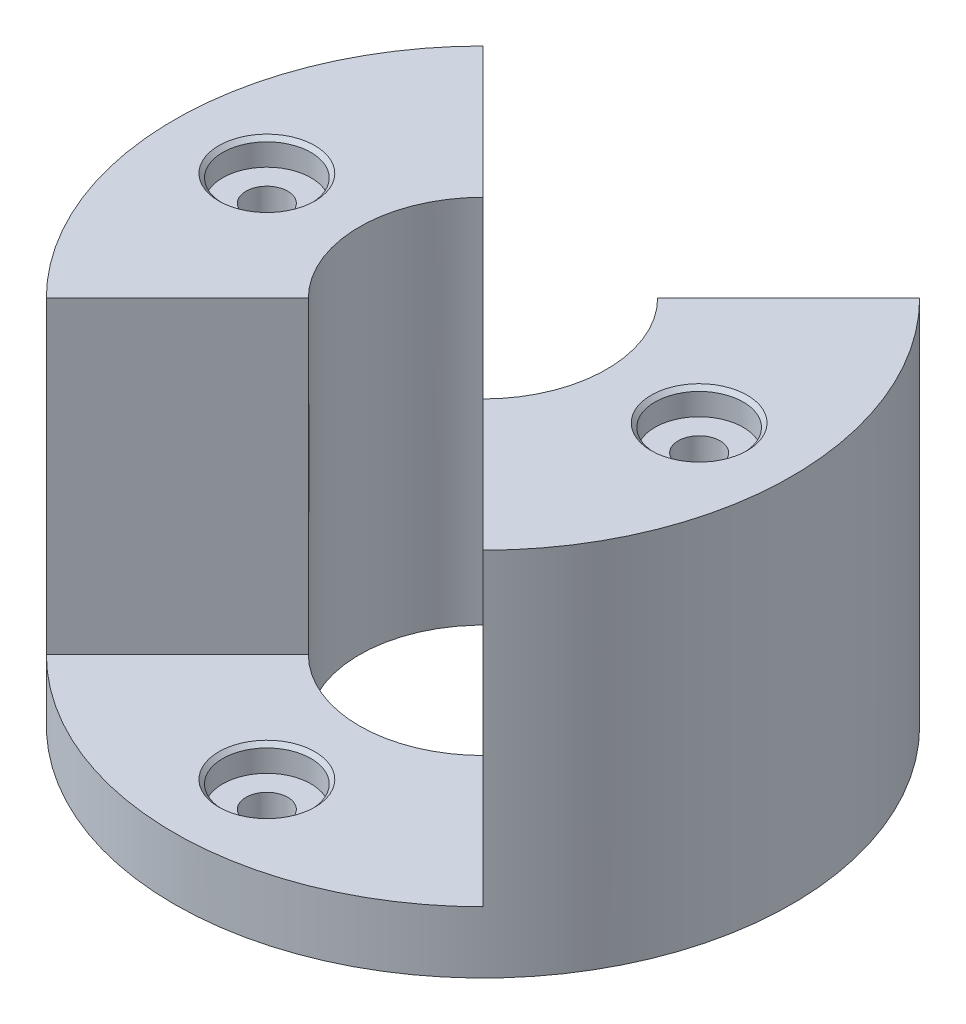
SolidWorks part; units mm, degrees
ref_plane "Front Plane" through (0, 0, 0) normal (0, 0, 1) x (1, 0, 0)
ref_plane "Top Plane" through (0, 0, 0) normal (0, 1, 0) x (1, 0, 0)
ref_plane "Right Plane" through (0, 0, 0) normal (1, 0, 0) x (0, 0, -1)
sketch "Sketch3" plane through (0, 0, 0) normal (0, 1, 0) x (1, 0, 0)
  circle A0 centre (0, 0) radius 50
extrude "Boss-Extrude1" add sketch "Sketch3" along normal blind 10
sketch "Sketch4" plane through (0, 10, 0) normal (0, 1, 0) x (1, 0, 0)
  circle A1 centre (0, 0) radius 20
extrude "Cut-Extrude3" cut sketch "Sketch4" against normal blind 10 contours A1
sketch "Sketch5" plane through (0, 10, 0) normal (0, 1, 0) x (1, 0, 0)
  line L0 (14.1421, -14.1421) -> (35.3553, -35.3553)
  line L1 (0, 0) -> (0, -28.103) construction
  line L2 (0, 0) -> (-17.4527, 0) construction
  line L3 (14.1421, 14.1421) -> (35.3553, 35.3553)
  line L4 (-14.1421, 14.1421) -> (-35.3553, 35.3553)
  line L5 (-14.1421, -14.1421) -> (-35.3553, -35.3553)
  circle A0 centre (0, 35) radius 5.7159
  circle A1 centre (0, 0) radius 50 construction
  arc A2 (-14.1421, -14.1421) -> (-14.1421, 14.1421) centre (0, 0) cw
  circle A3 centre (0, 0) radius 20 construction
  arc A4 (-35.3553, 35.3553) -> (-35.3553, -35.3553) centre (0, 0) ccw
  arc A5 (35.3553, -35.3553) -> (35.3553, 35.3553) centre (0, 0) ccw
  arc A6 (35.3553, 35.3553) -> (35.3553, -35.3553) centre (0, 0) cw
  arc A7 (14.1421, 14.1421) -> (14.1421, -14.1421) centre (0, 0) cw
  dimension "D1" = 35
extrude "Boss-Extrude3" add sketch "Sketch5" along normal blind 50 contours L3 L0 L1 | L5 L3 L4 L1
hole_wizard "CBORE for M6 Hex Head Bolt1" positions "Sketch6" profile "Sketch7" counterbore size "M6" standard "ANSI Metric" end condition through all
sketch "Sketch6" plane through (0, 60, 0) normal (0, 1, 0) x (1, 0, 0)
  line L0 (0, 0) -> (0, 51.3275) construction
  line L1 (0, 0) -> (0, -53.3889) construction
  line L3 (0, 0) -> (53.8699, 0) construction
  circle A0 centre (0, 0) radius 35 construction
  point P0 (-35, 0)
  point P2 (35, 0)
sketch "Sketch7" plane through (-35, 60, 0) normal (1, 0, 0) x (0, 0, 1)
  line L0 (0, 0) -> (0, 60)
  line L1 (0, 60) -> (3.38, 60)
  line L3 (3.38, 60) -> (3.38, 4.19)
  line L4 (7.145, 4.19) -> (3.38, 4.19)
  line L5 (7.145, 4.19) -> (7.145, 0.635)
  line L6 (7.145, 0.635) -> (7.78, 0)
  line L7 (7.78, 0) -> (0, 0)
  line L8 (-7.145, 0.635) -> (-7.78, 0) construction
  line L11 (0, -6.35) -> (0, 107.95) construction
  dimension "Thru Hole Dia." = 6.76
  dimension "Thru Hole Depth" = 60
  dimension "C'Bore Dia." = 14.29
  dimension "C'Bore Depth" = 4.19
  dimension "Near C'Sink Dia." = 15.56
  dimension "Near C'Sink Angle" = 90
hole_wizard "CBORE for M6 Hex Head Bolt4" positions "Sketch16" profile "Sketch17" counterbore size "M6" standard "ANSI Metric" end condition through all
sketch "Sketch16" plane through (0, 10, 0) normal (0, 1, 0) x (1, 0, 0)
  circle A0 centre (0, 0) radius 35 construction
  point P0 (0, 35)
  point P2 (0, -35)
  point P10 (0, 0)
  point P11 (0, 0)
sketch "Sketch17" plane through (0, 10, -35) normal (1, 0, 0) x (0, 0, 1)
  line L0 (0, 0) -> (0, 10)
  line L1 (0, 10) -> (3.38, 10)
  line L3 (3.38, 10) -> (3.38, 4.19)
  line L4 (7.145, 4.19) -> (3.38, 4.19)
  line L5 (7.145, 4.19) -> (7.145, 0.635)
  line L6 (7.145, 0.635) -> (7.78, 0)
  line L7 (7.78, 0) -> (0, 0)
  line L8 (-7.145, 0.635) -> (-7.78, 0) construction
  line L11 (0, -6.35) -> (0, 107.95) construction
  dimension "Thru Hole Dia." = 6.76
  dimension "Thru Hole Depth" = 10
  dimension "C'Bore Dia." = 14.29
  dimension "C'Bore Depth" = 4.19
  dimension "Near C'Sink Dia." = 15.56
  dimension "Near C'Sink Angle" = 90
